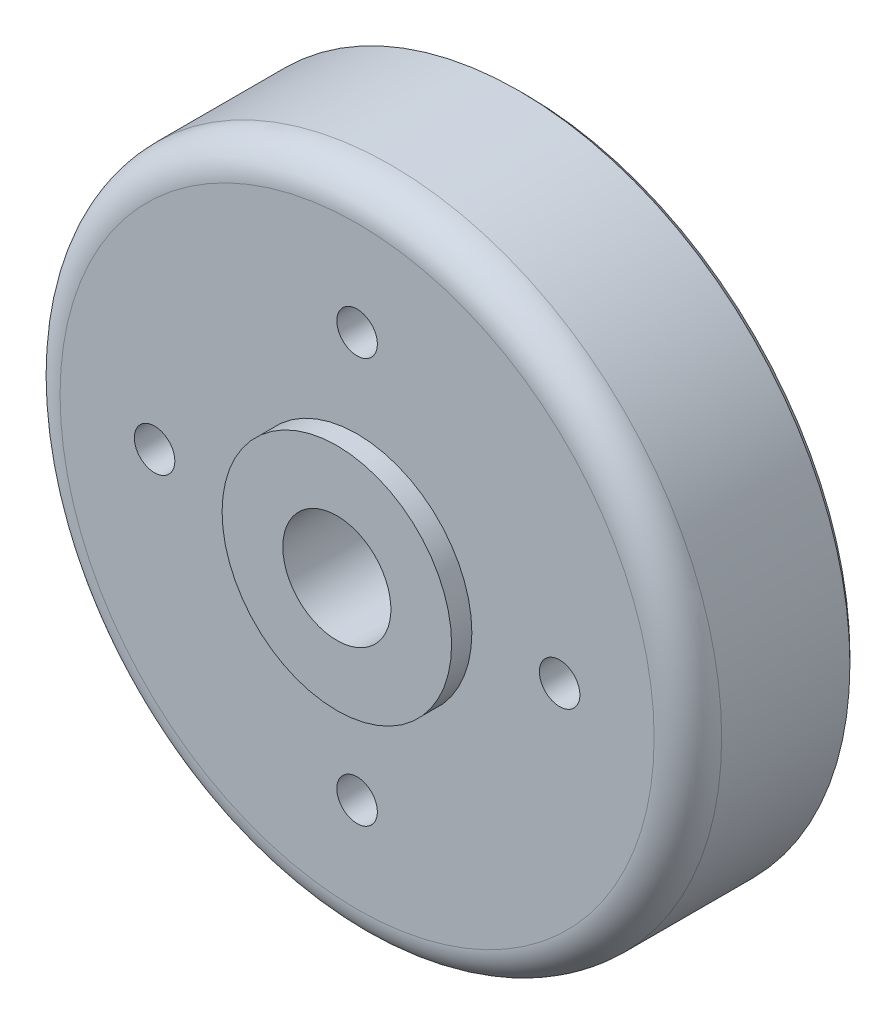
SolidWorks part; units mm, degrees
ref_plane "Front Plane" through (0, 0, 0) normal (0, 0, 1) x (1, 0, 0)
ref_plane "Top Plane" through (0, 0, 0) normal (0, 1, 0) x (1, 0, 0)
ref_plane "Right Plane" through (0, 0, 0) normal (1, 0, 0) x (0, 0, -1)
sketch "Sketch1" plane through (0, 0, 0) normal (0, 1, 0) x (1, 0, 0)
  line L0 (0, 29842.0772) -> (0, -44233.6084) construction
  line L1 (0, -29166.6667) -> (17000, -29166.6667)
  line L2 (17000, -29166.6667) -> (17000, -26166.6667)
  line L3 (17000, -26166.6667) -> (49000, -26166.6667)
  line L4 (49000, -26166.6667) -> (49000, -1166.6667)
  line L5 (49000, -1166.6667) -> (45000, -1166.6667)
  line L6 (45000, -1166.6667) -> (43000, -16166.6667)
  line L7 (43000, -16166.6667) -> (17000, -16166.6667)
  line L8 (17000, -16166.6667) -> (14000, 14833.3333)
  line L9 (14000, 14833.3333) -> (0, 14833.3333)
  line L10 (0, -29166.6667) -> (0, 14833.3333)
  point P12 (47000, -1166.6667)
  dimension "D1" = 17000
  dimension "D2" = 49000
  dimension "D3" = 4000
  dimension "D4" = 14000
  dimension "D5" = 43000
  dimension "D6" = 44000
  dimension "D7" = 25000
  dimension "D8" = 15000
  dimension "D9" = 28000
revolve "Revolve1" add sketch "Sketch1" angle 360 about L0
sketch "Sketch2" plane through (0, 0, -14833.3333) normal (0, 0, -1) x (-1, 0, 0)
  circle A0 centre (0, 0) radius 8000
  dimension "D1" = 16000
extrude "Cut-Extrude1" cut sketch "Sketch2" against normal blind 50000
sketch "Sketch4" plane through (0, 0, 26166.6667) normal (0, 0, 1) x (1, 0, 0)
  circle A0 centre (0, 0) radius 30000 construction
  circle A1 centre (0, 30000) radius 3000
  circle A2 centre (30000, 0) radius 3000
  circle A3 centre (0, -30000) radius 3000
  circle A4 centre (-30000, 0) radius 3000
  point P14 (0, 0)
  dimension "D1" = 60000
  dimension "D2" = 6000
  dimension "D3" = 4
extrude "Cut-Extrude2" cut sketch "Sketch4" against normal blind 50000
fillet "Fillet3" radius 5000 1 edges at (-49000, 0, 26166.6667)
fillet "Fillet4" radius 2000 1 edges at (-43000, 0, 16166.6667)
fillet "Fillet5" radius 2000 1 edges at (-14000, 0, -14833.3333)
chamfer "Chamfer1" distance 1000 angle 45 1 edges at (-49000, 0, 1166.6667)
